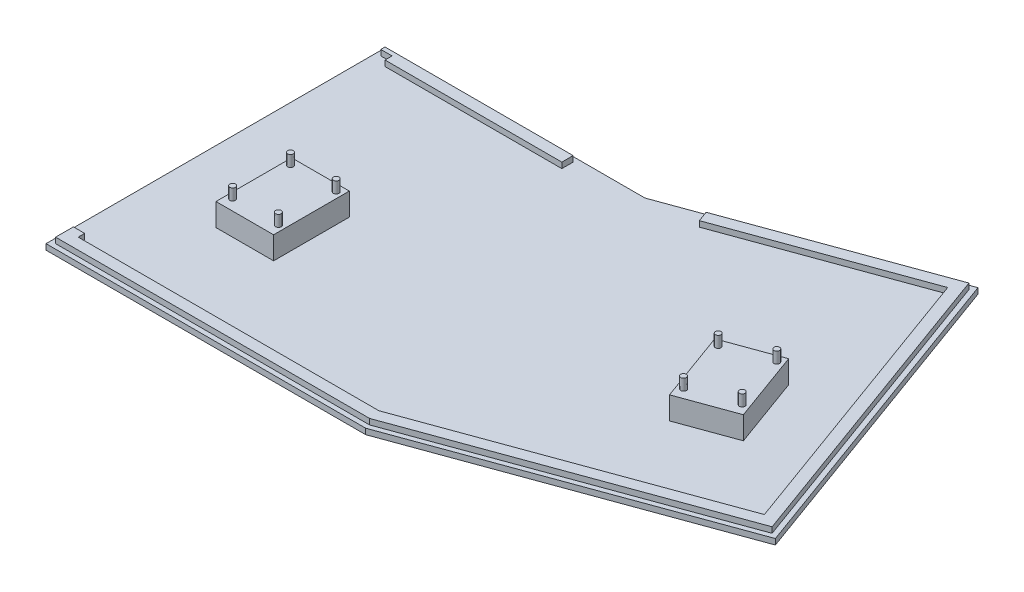
SolidWorks part; units mm, degrees
ref_plane "Front Plane" through (0, 0, 0) normal (0, 0, 1) x (1, 0, 0)
ref_plane "Top Plane" through (0, 0, 0) normal (0, 1, 0) x (1, 0, 0)
ref_plane "Right Plane" through (0, 0, 0) normal (1, 0, 0) x (0, 0, -1)
sketch "Sketch1" plane through (0, 0, 0) normal (0, 1, 0) x (1, 0, 0)
  line L0 (0, 0) -> (0, 152.4)
  line L1 (0, 152.4) -> (116.84, 152.4)
  line L2 (116.84, 152.4) -> (143.7093, 0.0165)
  line L3 (0, 0) -> (143.7093, 0.0165)
  dimension "D1" = 152.4
  dimension "D2" = 116.84
  dimension "D3" = 100
  dimension "D4" = 143.7093
extrude "Boss-Extrude1" add sketch "Sketch1" along normal blind 2.54 contours L3 L2 L1 L0
sketch "Sketch2" plane through (0, 2.54, 0) normal (0, 1, 0) x (1, 0, 0)
  line L0 (117.2207, 150.241) -> (2.159, 150.241)
  line L1 (116.84, 152.4) -> (143.7093, 0.0165) construction
  line L2 (2.159, 150.241) -> (2.159, 2.159)
  line L3 (2.159, 2.159) -> (143.3315, 2.159)
  line L4 (0, 152.4) -> (116.84, 152.4) construction
  line L5 (0, 0) -> (0, 152.4) construction
  line L8 (118.1164, 145.161) -> (7.239, 145.161)
  line L9 (7.239, 145.161) -> (7.239, 7.239)
  line L10 (7.239, 7.239) -> (142.4358, 7.239)
  line L11 (117.2207, 150.241) -> (118.1164, 145.161)
  line L12 (142.4358, 7.239) -> (143.3315, 2.159)
  dimension "D1" = 2.159
  dimension "D2" = 2.159
  dimension "D3" = 148.082
  dimension "D4" = 5.08
  dimension "D5" = 5.08
  dimension "D6" = 5.08
extrude "Boss-Extrude2" add sketch "Sketch2" along normal blind 2.54 contours L12 L3 L2 L0 L11 L8 L9 L10
sketch "Sketch5" plane through (0, 0, 0) normal (0, -1, 0) x (1, 0, 0)
  line L0 (0, -78.4957) -> (77.4538, -78.4957) construction
  line L1 (0, -152.4) -> (116.84, -152.4) construction
  line L2 (31.9519, -78.4957) -> (31.9519, -39.2242) construction
  line L3 (0, 0) -> (0, -152.4) construction
  line L5 (31.9519, -78.4957) -> (57.8599, -78.4957)
  line L6 (31.9519, -78.4957) -> (31.9519, -44.4597)
  line L7 (31.9519, -44.4597) -> (57.8599, -44.4597)
  line L8 (57.8599, -78.4957) -> (57.8599, -44.4597)
  dimension "D1" = 73.9043
  dimension "D2" = 31.9519
  dimension "D3" = 25.908
  dimension "D4" = 34.036
extrude "Boss-Extrude3" add sketch "Sketch5" against normal blind 12.7 contours L6 L5 L8 L7
sketch "Sketch6" plane through (0, 12.7, 0) normal (0, 1, 0) x (1, 0, 0)
  line L0 (36.2762, 78.4948) -> (36.2762, 44.4588) construction
  line L1 (53.5482, 78.4948) -> (53.5482, 44.4588) construction
  line L2 (31.9582, 73.6688) -> (57.8662, 73.6688) construction
  line L3 (31.9582, 50.8088) -> (57.8662, 50.8088) construction
  line L4 (31.9582, 76.9708) -> (57.8662, 76.9708) construction
  line L5 (31.9582, 47.7608) -> (57.8662, 47.7608) construction
  line L6 (32.9742, 78.4948) -> (32.9742, 44.4588) construction
  line L7 (56.8502, 78.4948) -> (56.8502, 44.4588) construction
  line L8 (32.9742, 76.9708) -> (36.2762, 73.6688) construction
  line L9 (36.2762, 76.9708) -> (32.9742, 73.6688) construction
  line L10 (53.5482, 76.9708) -> (56.8502, 73.6688) construction
  line L11 (56.8502, 76.9708) -> (53.5482, 73.6688) construction
  line L12 (36.2762, 50.8088) -> (32.9742, 47.7608) construction
  line L13 (32.9742, 50.8088) -> (36.2762, 47.7608) construction
  line L14 (56.8502, 50.8088) -> (53.5482, 47.7608) construction
  line L15 (53.5482, 50.8088) -> (56.8502, 47.7608) construction
  circle A0 centre (34.6252, 75.3198) radius 1.27
  circle A1 centre (55.17, 75.2906) radius 1.27
  circle A2 centre (55.1992, 49.2848) radius 1.27
  circle A3 centre (34.6252, 49.2848) radius 1.27
extrude "Boss-Extrude4" add sketch "Sketch6" along normal blind 5.08
mirror "Mirror2" about plane through (116.84, 2.54, -152.4) normal (0.9848, 0, -0.1736) of bodies 105
sketch "Sketch7" plane through (0, 5.08, 0) normal (0, 1, 0) x (1, 0, 0)
  line L0 (2.159, 150.241) -> (2.159, 2.159) construction
  line L1 (2.159, 148.336) -> (7.239, 148.336)
  line L2 (2.159, 148.336) -> (2.159, 10.16)
  line L3 (2.159, 10.16) -> (7.239, 10.16)
  line L4 (7.239, 148.336) -> (7.239, 10.16)
  line L5 (7.239, 145.161) -> (7.239, 7.239) construction
  line L6 (0, 152.4) -> (116.84, 152.4) construction
  dimension "D1" = 4.064
  dimension "D2" = 142.24
extrude "Cut-Extrude1" cut sketch "Sketch7" against normal blind 2.54
sketch "Sketch8" plane through (0, 5.08, 0) normal (0, 1, 0) x (1, 0, 0)
  line L0 (86.7407, 150.241) -> (86.7407, 145.161)
  line L1 (117.2207, 150.241) -> (2.159, 150.241) construction
  line L2 (118.1164, 145.161) -> (7.239, 145.161) construction
  line L3 (138.7021, 158.0596) -> (140.4395, 153.2859)
  line L4 (117.2207, 150.241) -> (225.3433, 189.5944) construction
  line L5 (118.1164, 145.161) -> (222.3071, 183.0833) construction
  line L6 (86.7407, 150.241) -> (117.2207, 150.241)
  line L7 (117.2207, 150.241) -> (138.7021, 158.0596)
  line L8 (140.4395, 153.2859) -> (118.1164, 145.161)
  line L9 (118.1164, 145.161) -> (86.7407, 145.161)
  dimension "D1" = 30.48
  dimension "D2" = 22.86
extrude "Cut-Extrude2" cut sketch "Sketch8" against normal blind 2.54
